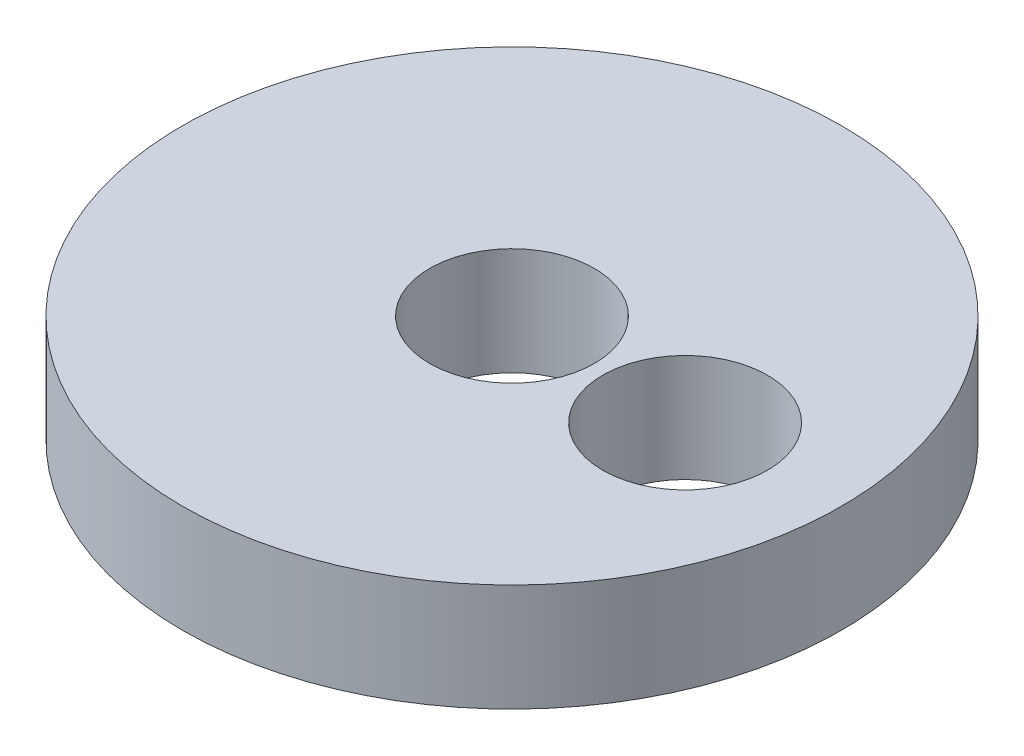
SolidWorks part; units mm, degrees
ref_plane "Front Plane" through (0, 0, 0) normal (0, 0, 1) x (1, 0, 0)
ref_plane "Top Plane" through (0, 0, 0) normal (0, 1, 0) x (1, 0, 0)
ref_plane "Right Plane" through (0, 0, 0) normal (1, 0, 0) x (0, 0, -1)
sketch "Sketch1" plane through (0, 0, 0) normal (0, 1, 0) x (1, 0, 0)
  circle A0 centre (0, 0) radius 9.2
  circle A1 centre (4.9973, -0.1648) radius 2.3
  circle A2 centre (0, 0) radius 2.3
  dimension "D1" = 18.4
  dimension "D3" = 4.6
  dimension "D4" = 4.6
  dimension "D2" = 4.9973
extrude "Boss-Extrude1" add sketch "Sketch1" along normal blind 3
